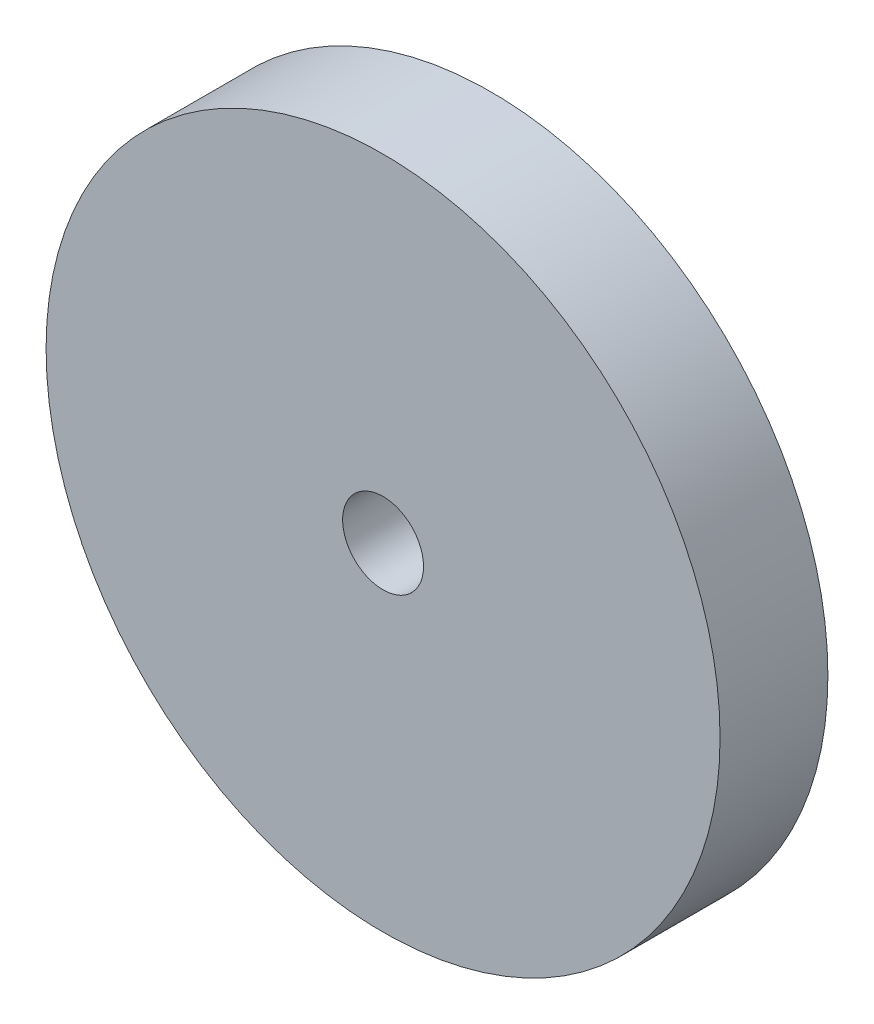
SolidWorks part; units mm, degrees
ref_plane "Спереди" through (0, 0, 0) normal (0, 0, 1) x (1, 0, 0)
ref_plane "Сверху" through (0, 0, 0) normal (0, 1, 0) x (1, 0, 0)
ref_plane "Справа" through (0, 0, 0) normal (1, 0, 0) x (0, 0, -1)
sketch "Эскиз1" plane through (0, 0, 0) normal (0, 0, 1) x (1, 0, 0)
  circle A0 centre (0, 0) radius 12.5
  circle A1 centre (0, 0) radius 1.5
  dimension "D1" = 25
  dimension "D2" = 3
extrude "Бобышка-Вытянуть1" add sketch "Эскиз1" along normal blind 4
